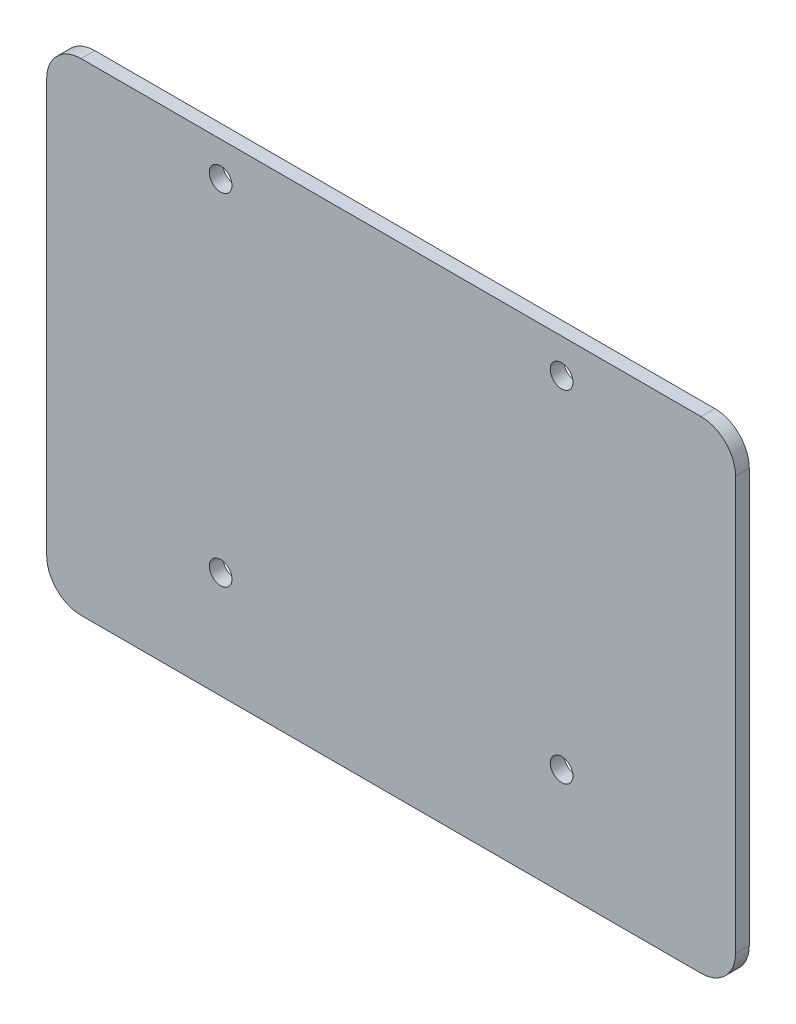
SolidWorks part; units mm, degrees
ref_plane "前视基准面" through (0, 0, 0) normal (0, 0, 1) x (1, 0, 0)
ref_plane "上视基准面" through (0, 0, 0) normal (0, 1, 0) x (1, 0, 0)
ref_plane "右视基准面" through (0, 0, 0) normal (1, 0, 0) x (0, 0, -1)
sketch "草图1" plane through (0, 0, 0) normal (0, 0, 1) x (1, 0, 0)
  line L0 (50, 70) -> (50, 0) construction
  line L1 (0, 0) -> (100, 0)
  line L2 (0, 0) -> (0, 70)
  line L3 (0, 70) -> (100, 70)
  line L4 (100, 0) -> (100, 70)
  line L5 (25.25, 70) -> (25.25, 0) construction
  circle A0 centre (25.25, 65) radius 1.65
  circle A1 centre (25.25, 15.5) radius 1.65
  circle A2 centre (74.75, 15.5) radius 1.65
  circle A3 centre (74.75, 65) radius 1.65
  dimension "D4" = 3.3
  dimension "D5" = 3.3
  dimension "D1" = 70
  dimension "D2" = 100
  dimension "D3" = 24.75
  dimension "D6" = 5
  dimension "D7" = 49.5
  dimension "D8" = 15.5
extrude "凸台-拉伸1" add sketch "草图1" along normal blind 2
fillet "圆角1" radius 5 4 edges at (0, 70, 1) (100, 70, 1) (100, 0, 1) (0, 0, 1)
